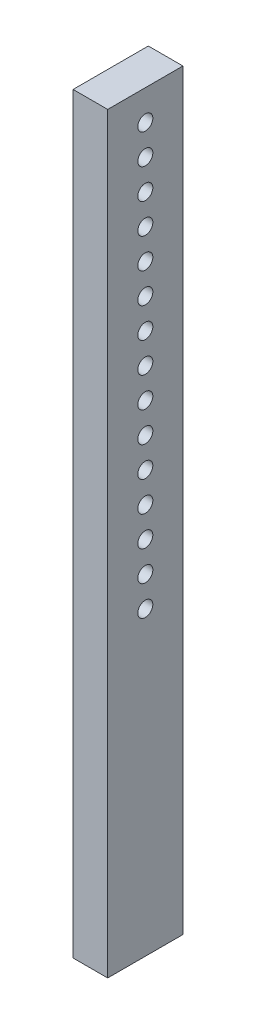
SolidWorks part; units mm, degrees
ref_plane "Front Plane" through (0, 0, 0) normal (0, 0, 1) x (1, 0, 0)
ref_plane "Top Plane" through (0, 0, 0) normal (0, 1, 0) x (1, 0, 0)
ref_plane "Right Plane" through (0, 0, 0) normal (1, 0, 0) x (0, 0, -1)
sketch "Sketch1" plane through (0, 0, 0) normal (1, 0, 0) x (0, 0, -1)
  line L0 (0, 277.8706) -> (0, -275.6832) construction
  line L1 (-25, 250) -> (25, 250)
  line L2 (-25, 250) -> (-25, -250)
  line L3 (-25, -250) -> (25, -250)
  line L4 (25, 250) -> (25, -250)
  line L5 (-25, 250) -> (25, -250) construction
  line L6 (-25, -250) -> (25, 250) construction
  circle A0 centre (0, 230) radius 5
  circle A1 centre (0, 210) radius 5
  circle A2 centre (0, 190) radius 5
  circle A3 centre (0, 170) radius 5
  circle A4 centre (0, 150) radius 5
  circle A5 centre (0, 130) radius 5
  circle A6 centre (0, 110) radius 5
  circle A7 centre (0, 90) radius 5
  circle A8 centre (0, 70) radius 5
  circle A9 centre (0, 50) radius 5
  circle A10 centre (0, 30) radius 5
  circle A11 centre (0, 10) radius 5
  circle A12 centre (0, -10) radius 5
  circle A13 centre (0, -30) radius 5
  circle A14 centre (0, -50) radius 5
  point P0 (0, 0)
  dimension "D3" = 10
  dimension "D1" = 500
  dimension "D2" = 50
  dimension "D4" = 20
  dimension "D5" = 15
extrude "Boss-Extrude1" add sketch "Sketch1" along normal blind 23
